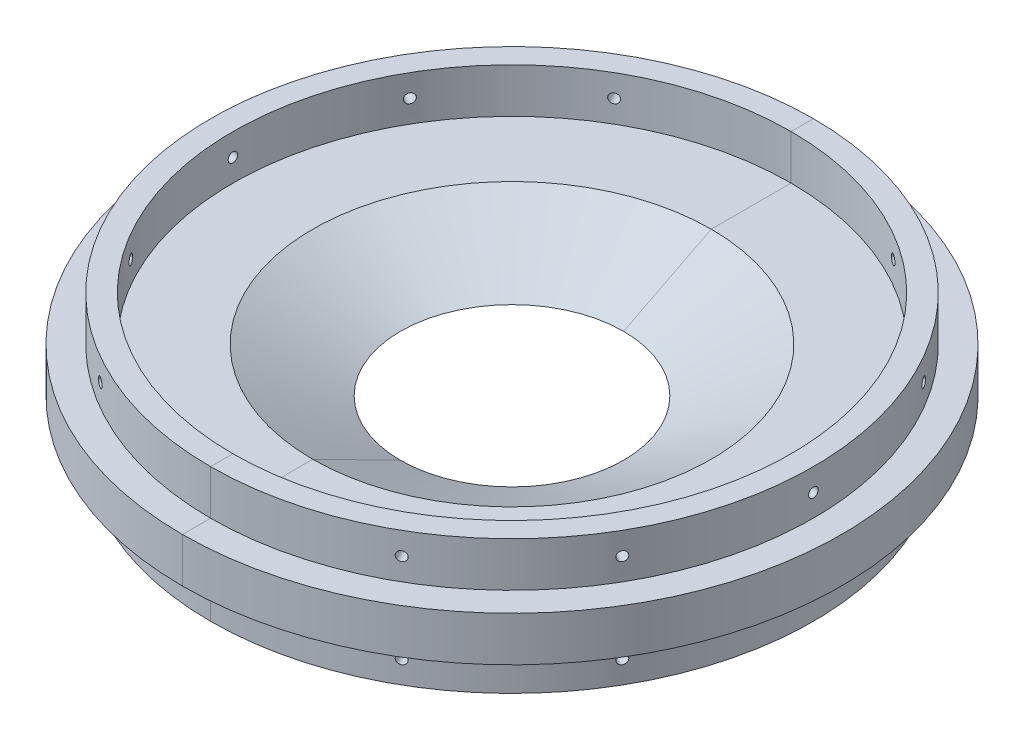
SolidWorks part; units mm, degrees
ref_plane "Front Plane" through (0, 0, 0) normal (0, 0, 1) x (1, 0, 0)
ref_plane "Top Plane" through (0, 0, 0) normal (0, 1, 0) x (1, 0, 0)
ref_plane "Right Plane" through (0, 0, 0) normal (1, 0, 0) x (0, 0, -1)
sketch "Sketch1" plane through (0, 0, 0) normal (0, 1, 0) x (1, 0, 0)
  circle A0 centre (0, 0) radius 93.726
  circle A1 centre (0, 0) radius 31.75
  dimension "D1" = 187.452
  dimension "D2" = 63.5
extrude "Boss-Extrude1" add sketch "Sketch1" along normal mid plane 12.7
sketch "Sketch5" plane through (0, 6.35, 0) normal (0, 1, 0) x (1, 0, 0)
  circle A0 centre (0, 0) radius 85.725
  circle A1 centre (0, 0) radius 79.375
  dimension "D1" = 171.45
  dimension "D2" = 158.75
extrude "Boss-Extrude2" add sketch "Sketch5" along normal blind 12.7
ref_plane "Plane1" through (0, 0, -85.725) normal (0, 0, -1) x (-1, 0, 0)
sketch "Sketch6" plane through (0, 0, -85.725) normal (0, 0, -1) x (-1, 0, 0)
  line L0 (0, 13.97) -> (0, -13.97) construction
  line L1 (93.726, 6.35) -> (-93.726, 6.35) construction
  circle A0 centre (0, 12.7) radius 1.3525
  dimension "D1" = 2.7051
  dimension "D2" = 6.35
extrude "Cut-Extrude1" cut sketch "Sketch6" against normal blind 12.7
pattern_circular "CirPattern1" count 12 over 360 about axis through (0, 6.35, 0) along (0, -1, 0) of "Cut-Extrude1"
mirror "Mirror1" about plane through (0, 0, 0) normal (0, 1, 0) of "CirPattern1", "Cut-Extrude1", "Boss-Extrude2"
sketch "Sketch7" plane through (0, 19.05, 0) normal (0, 1, 0) x (1, 0, 0)
  line L0 (-25.7878, 75.0692) -> (-28.1663, 80.9657)
  line L1 (28.1663, 80.9657) -> (25.7878, 75.0692)
  arc A0 (28.1663, 80.9657) -> (-28.1663, 80.9657) centre (0, 0) ccw
  circle A1 centre (0, 0) radius 85.725 construction
  arc A2 (25.7878, 75.0692) -> (-25.7878, 75.0692) centre (0, 0) ccw
  circle A3 centre (0, 0) radius 79.375 construction
extrude "Boss-Extrude3" add sketch "Sketch7" against normal up to surface (25.4 mm away)
mirror "Mirror3" about plane through (0, 0, 0) normal (0, 1, 0) of "Boss-Extrude3"
mirror "Mirror4" about plane through (0, 0, 0) normal (0, 0, 1) of "Boss-Extrude3"
mirror "Mirror5" about plane through (0, 0, 0) normal (0, 1, 0) of "Mirror4"
sketch "Sketch4" plane through (0, 0, 0) normal (0, 0, 1) x (1, 0, 0)
  line L0 (0, 23.2786) -> (0, -14.9525) construction
sketch "Sketch3" plane through (0, 0, 0) normal (0, 0, 1) x (1, 0, 0)
  line L0 (-31.75, -6.35) -> (-56.6752, 6.35)
  line L1 (93.726, 6.35) -> (-93.726, 6.35) construction
  line L2 (-56.6752, 6.35) -> (-31.75, 6.35)
  line L3 (-31.75, 6.35) -> (-31.75, -6.35)
  line L4 (-31.75, -6.35) -> (31.75, -6.35) construction
  line L6 (31.75, 6.35) -> (-31.75, 6.35) construction
  dimension "D1" = 27
revolve "Cut-Revolve1" cut sketch "Sketch3" angle 360 about L0
split "Split1" trim tools "Right Plane" bodies to split 103 resulting bodies 104 105
